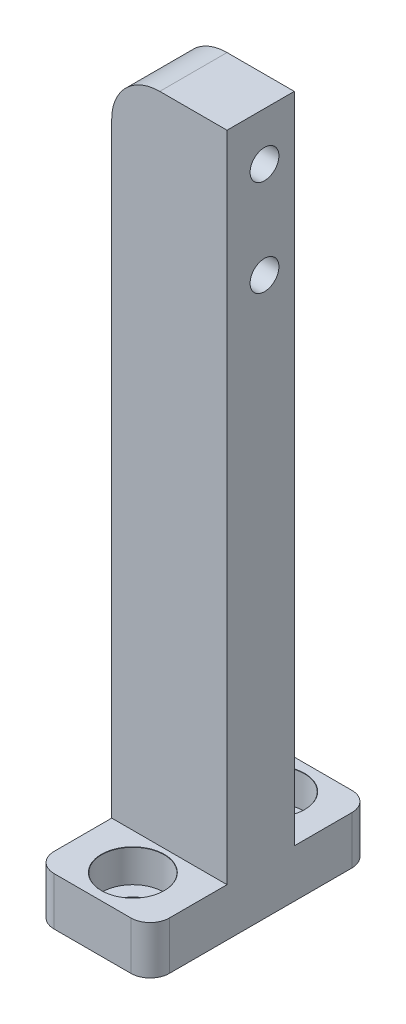
SolidWorks part; units mm, degrees
ref_plane "Front Plane" through (0, 0, 0) normal (0, 0, 1) x (1, 0, 0)
ref_plane "Top Plane" through (0, 0, 0) normal (0, 1, 0) x (1, 0, 0)
ref_plane "Right Plane" through (0, 0, 0) normal (1, 0, 0) x (0, 0, -1)
sketch "Sketch1" plane through (0, 0, 0) normal (0, 1, 0) x (1, 0, 0)
  line L1 (-6, -3.5) -> (6, -3.5)
  line L2 (-6, -3.5) -> (-6, 3.5)
  line L3 (-6, 3.5) -> (6, 3.5)
  line L4 (6, -3.5) -> (6, 3.5)
  line L5 (-6, -3.5) -> (6, 3.5) construction
  line L6 (-6, 3.5) -> (6, -3.5) construction
  point P0 (0, 0)
  dimension "D1" = 7
  dimension "D2" = 12
extrude "Boss-Extrude1" add sketch "Sketch1" along normal mid plane 73
sketch "Sketch3" plane through (0, 0, 0) normal (0, 0, 1) x (1, 0, 0)
  line L0 (-6, 36.5) -> (-6, -36.5) construction
  line L1 (-6, -31.5) -> (6, -31.5)
  line L2 (-6, -31.5) -> (-6, -36.5)
  line L3 (-6, -36.5) -> (6, -36.5)
  line L4 (6, -31.5) -> (6, -36.5)
  dimension "D1" = 5
extrude "Boss-Extrude2" add sketch "Sketch3" along normal mid plane 23
fillet "Fillet1" radius 2 4 edges at (-6, -34, -11.5) (6, -34, -11.5) (-6, -34, 11.5) (6, -34, 11.5)
hole_wizard "CBORE for M3 Hex Socket Head Cap Screw1" positions "Sketch4" profile "Sketch6" counterbore size "M3" standard "DIN" end condition through all
sketch "Sketch4" plane through (0, -31.5, 0) normal (0, 1, 0) x (1, 0, 0)
  line L0 (6, 3.5) -> (-6, 3.5) construction
  point P0 (0, 7.3)
  dimension "D1" = 3.8
sketch "Sketch6" plane through (0, -31.5, -7.3) normal (1, 0, 0) x (0, 0, 1)
  line L0 (0, 0) -> (0, 5)
  line L1 (0, 5) -> (1.7, 5)
  line L3 (1.7, 5) -> (1.7, 3.4)
  line L4 (3.25, 3.4) -> (1.7, 3.4)
  line L5 (3.25, 3.4) -> (3.25, 0.025)
  line L6 (3.25, 0.025) -> (3.275, 0)
  line L7 (3.275, 0) -> (0, 0)
  line L8 (-3.25, 0.025) -> (-3.275, 0) construction
  line L11 (0, -6.35) -> (0, 107.95) construction
  dimension "Thru Hole Dia." = 3.4
  dimension "Thru Hole Depth" = 5
  dimension "C'Bore Dia." = 6.5
  dimension "C'Bore Depth" = 3.4
  dimension "Near C'Sink Dia." = 6.55
  dimension "Near C'Sink Angle" = 90
mirror "Mirror1" about plane through (0, 0, 0) normal (0, 0, 1) of "CBORE for M3 Hex Socket Head Cap Screw1"
fillet "Fillet2" radius 5 1 edges at (-6, 36.5, 0)
sketch "Sketch7" plane through (6, 0, 0) normal (1, 0, 0) x (0, 0, -1)
  line L0 (-3.5, 36.5) -> (3.5, 36.5) construction
  line L2 (3.5, 36.5) -> (3.5, -31.5) construction
  circle A0 centre (0.4, 31.5) radius 1.5
  circle A1 centre (0.4, 21.5) radius 1.5
  dimension "D1" = 3
  dimension "D2" = 5
  dimension "D3" = 10
  dimension "D4" = 3.1
extrude "Cut-Extrude1" cut sketch "Sketch7" against normal up to next
